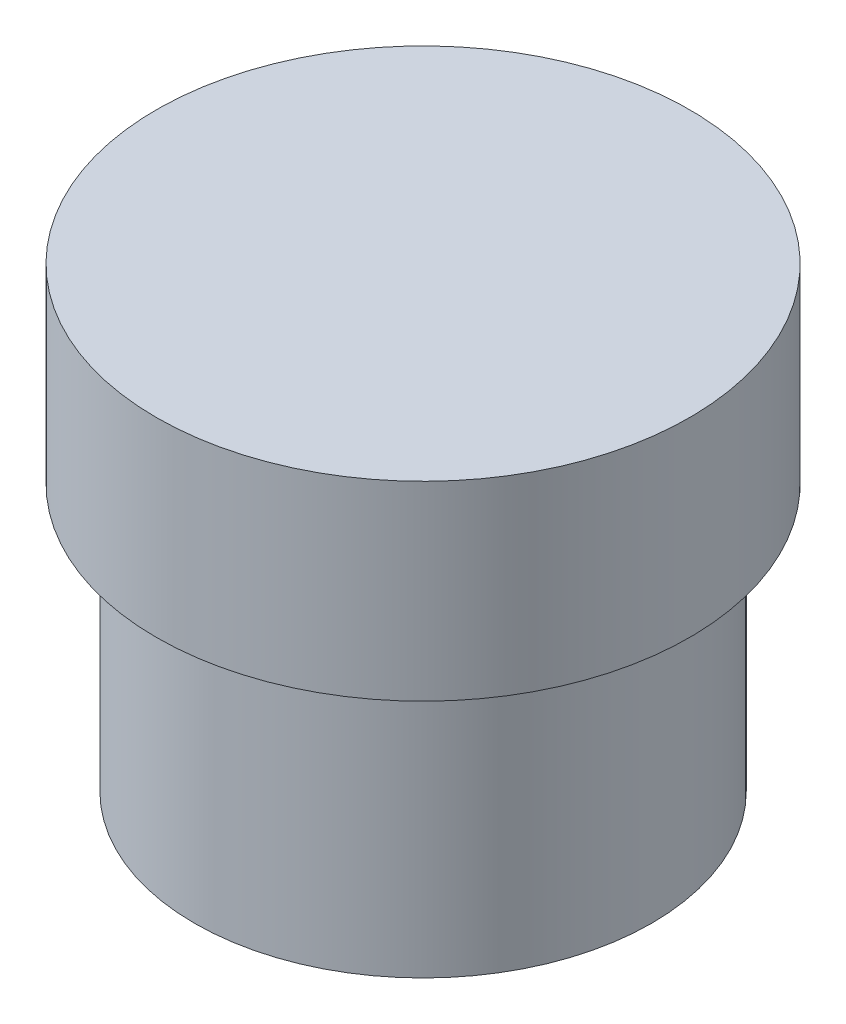
SolidWorks part; units mm, degrees
ref_plane "前视基准面" through (0, 0, 0) normal (0, 0, 1) x (1, 0, 0)
ref_plane "上视基准面" through (0, 0, 0) normal (0, 1, 0) x (1, 0, 0)
ref_plane "右视基准面" through (0, 0, 0) normal (1, 0, 0) x (0, 0, -1)
sketch "草图1" plane through (0, 0, 0) normal (0, 1, 0) x (1, 0, 0)
  circle A0 centre (0, 0) radius 7
extrude "凸台-拉伸2" add sketch "草图1" against normal blind 5
sketch "草图3" plane through (0, -5, 0) normal (0, -1, 0) x (-1, 0, 0)
  circle A0 centre (0, 0) radius 6
extrude "凸台-拉伸3" add sketch "草图3" along normal blind 7 contours A0
